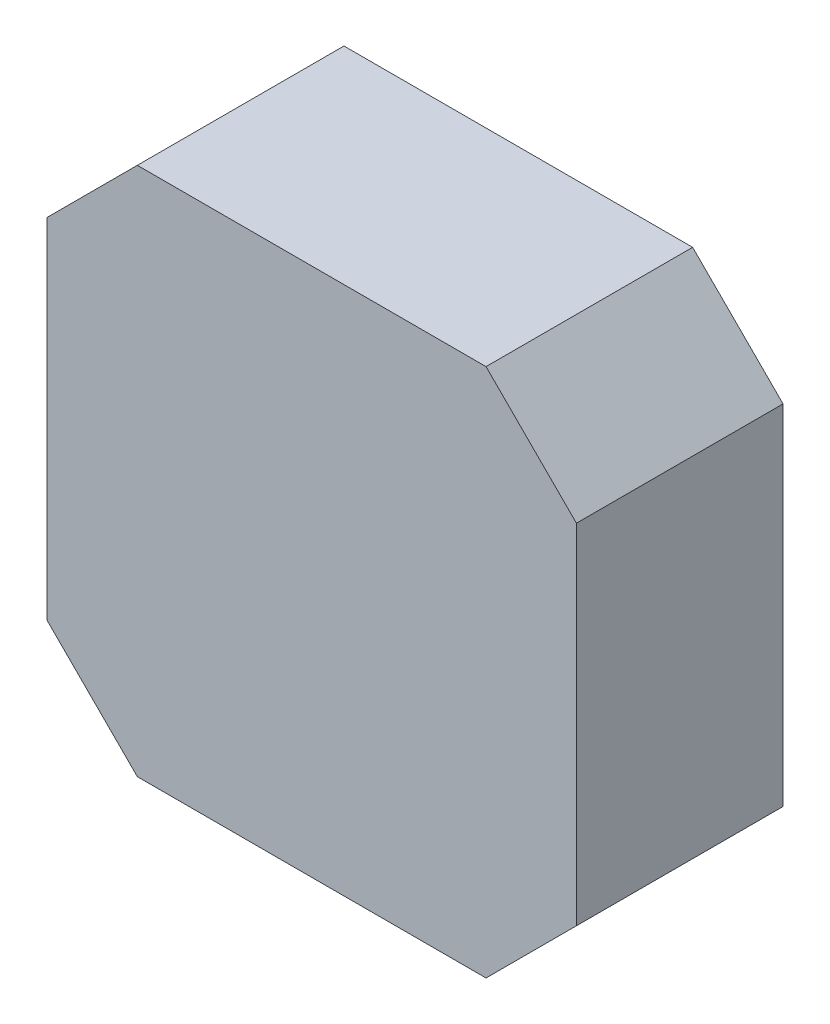
SolidWorks part; units mm, degrees
material "Acero aleado"
ref_plane "Alzado" through (0, 0, 0) normal (0, 0, 1) x (1, 0, 0)
ref_plane "Planta" through (0, 0, 0) normal (0, 1, 0) x (1, 0, 0)
ref_plane "Vista lateral" through (0, 0, 0) normal (1, 0, 0) x (0, 0, -1)
sketch "Croquis1" plane through (0, 0, 0) normal (0, 0, 1) x (1, 0, 0)
  line L0 (-13.5, 20.5) -> (-20.5, 13.5)
  line L1 (-13.5, 20.5) -> (13.5, 20.5)
  line L2 (-20.5, 13.5) -> (-20.5, -13.5)
  line L3 (-13.5, -20.5) -> (13.5, -20.5)
  line L4 (20.5, 13.5) -> (20.5, -13.5)
  line L5 (-20.5, 20.5) -> (20.5, -20.5) construction
  line L6 (-20.5, -20.5) -> (20.5, 20.5) construction
  line L7 (13.5, 20.5) -> (20.5, 13.5)
  line L8 (20.5, -13.5) -> (13.5, -20.5)
  line L9 (-20.5, -13.5) -> (-13.5, -20.5)
  point P0 (0, 0)
  dimension "D1" = 41
  dimension "D2" = 41
extrude "Saliente-Extruir1" add sketch "Croquis1" along normal blind 16
